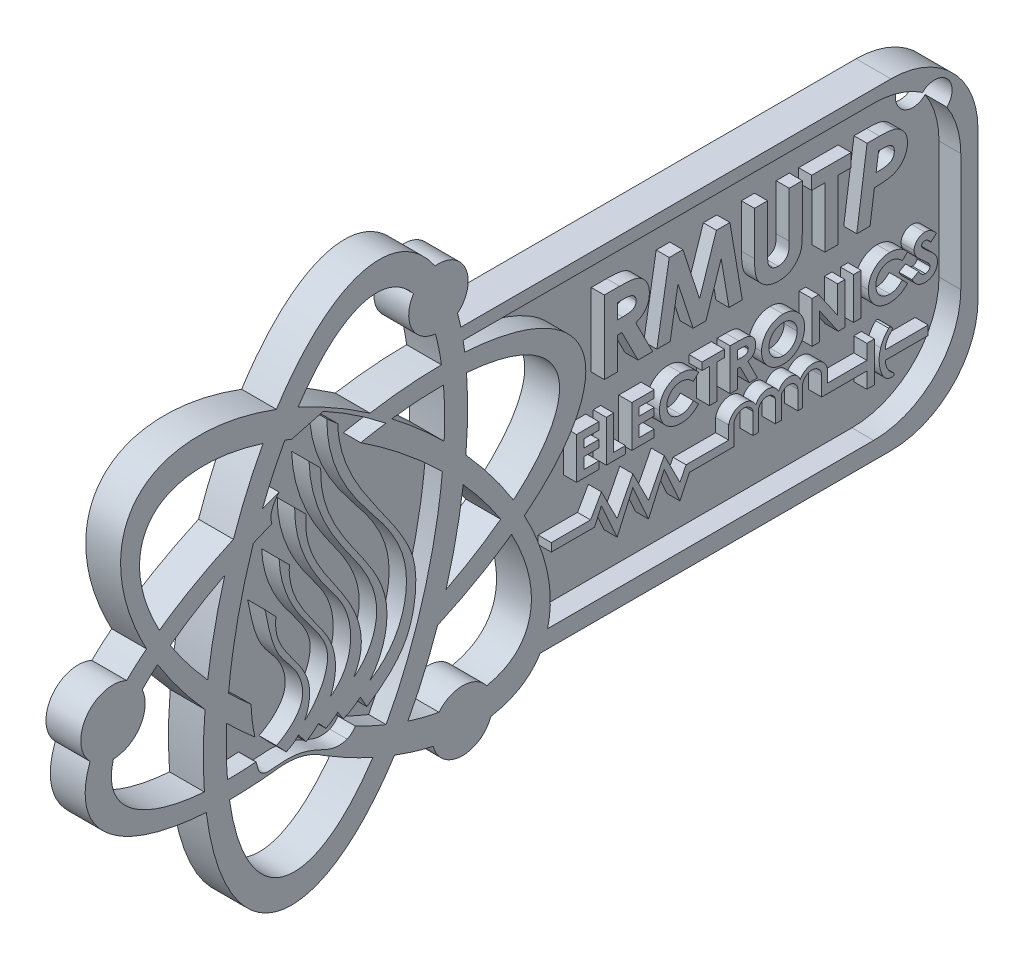
SolidWorks part; units mm, degrees
ref_plane "Front Plane" through (0, 0, 0) normal (0, 0, 1) x (1, 0, 0)
ref_plane "Top Plane" through (0, 0, 0) normal (0, 1, 0) x (1, 0, 0)
ref_plane "Right Plane" through (0, 0, 0) normal (1, 0, 0) x (0, 0, -1)
sketch "Sketch1" plane through (0, 0, 0) normal (1, 0, 0) x (0, 0, -1)
  line L0 (23.6962, 46.7228) -> (27.3509, 47.6931)
  line L1 (21.9568, 17.1343) -> (23.0925, 15.9422)
  line L2 (21.9056, 29.9851) -> (20.6519, 31.301)
  line L3 (24.4923, 16.9403) -> (25.3704, 15.8154)
  line L4 (23.4377, 34.3906) -> (22.2663, 35.562)
  line L5 (26.7972, 16.9366) -> (27.6441, 16.0073)
  line L6 (25.3704, 38.4449) -> (24.0506, 39.7647)
  line L7 (29.0048, 16.9366) -> (29.6488, 15.9422)
  line L8 (27.0464, 42.1977) -> (25.7038, 43.5403)
  line L9 (31.5987, 17.1343) -> (32.348, 15.8154)
  line L10 (29.0048, 45.6308) -> (27.7564, 46.7228)
  line L11 (92.5343, 48.1604) -> (43.1353, 48.1604)
  line L12 (43.3991, 46.7228) -> (90.5555, 46.7228)
  line L13 (53.1032, 13.1936) -> (90.5555, 13.1936)
  line L14 (92.5343, 11.1778) -> (52.2536, 11.1778)
  line L15 (100.5555, 36.7228) -> (100.5555, 23.1936)
  line L16 (102.5343, 38.1604) -> (102.5343, 21.1778)
  line L17 (54.5274, 20.5402) -> (59.0384, 20.5402)
  line L18 (59.0384, 20.5402) -> (60.2828, 22.7138)
  line L19 (60.2828, 22.7138) -> (62.0872, 19.1481)
  line L20 (62.0872, 19.1481) -> (63.8916, 22.7138)
  line L21 (63.8916, 22.7138) -> (65.696, 19.1481)
  line L22 (65.696, 19.1481) -> (67.5004, 22.7138)
  line L23 (67.5004, 22.7138) -> (69.3048, 19.1481)
  line L24 (69.3048, 19.1481) -> (70.0092, 20.5402)
  line L25 (70.0092, 20.5402) -> (74.9046, 20.5402)
  line L26 (74.9046, 20.5402) -> (74.9046, 22.0506)
  line L27 (86.2271, 22.0402) -> (86.2271, 20.5402)
  line L28 (86.2271, 20.5402) -> (90.7709, 20.5402)
  line L29 (90.7709, 20.5402) -> (90.7709, 22.2398)
  line L30 (90.7709, 22.2398) -> (91.6419, 22.2398)
  line L31 (91.6419, 22.2398) -> (91.6419, 17.6666)
  line L32 (91.6419, 17.6666) -> (90.7709, 17.6666)
  line L33 (90.7709, 17.6666) -> (90.7709, 19.4944)
  line L34 (90.7709, 19.4944) -> (85.5754, 19.4944)
  line L35 (85.5754, 19.4944) -> (85.5754, 21.6328)
  line L36 (83.3666, 21.6328) -> (83.3666, 19.4944)
  line L37 (83.3666, 19.4944) -> (82.8377, 19.4944)
  line L38 (82.8377, 19.4944) -> (82.8377, 21.6328)
  line L39 (80.94, 22.016) -> (80.94, 19.4944)
  line L40 (80.94, 19.4944) -> (80.2556, 19.4944)
  line L41 (80.2556, 19.4944) -> (80.2556, 22.016)
  line L42 (78.3521, 22.016) -> (78.3521, 19.5952)
  line L43 (78.3521, 19.5952) -> (77.6963, 19.5952)
  line L44 (77.6963, 19.5952) -> (77.6963, 22.016)
  line L45 (75.5169, 22.016) -> (75.5169, 19.5952)
  line L46 (75.5169, 19.5952) -> (70.395, 19.5952)
  line L47 (70.395, 19.5952) -> (69.3048, 17.2964)
  line L48 (69.3048, 17.2964) -> (67.5004, 21.3428)
  line L49 (67.5004, 21.3428) -> (65.696, 17.2964)
  line L50 (65.696, 17.2964) -> (63.8916, 21.3428)
  line L51 (63.8916, 21.3428) -> (62.0872, 17.2964)
  line L52 (62.0872, 17.2964) -> (60.2828, 21.3428)
  line L53 (60.2828, 21.3428) -> (59.5035, 19.5952)
  line L54 (59.5035, 19.5952) -> (54.5274, 19.5952)
  line L55 (54.5274, 19.5952) -> (54.5274, 20.5402)
  line L56 (97.8121, 20.5402) -> (97.8121, 19.4944)
  line L57 (97.8121, 19.4944) -> (92.8938, 19.494)
  line L58 (97.8121, 20.5402) -> (92.8938, 20.5402)
  circle A0 centre (3.1888, 28.8629) radius 3.6979
  circle A1 centre (40.5669, 52.343) radius 3.415
  circle A2 centre (43.3293, 8.9222) radius 3.4798
  arc A3 (74.9046, 22.0506) -> (78.0389, 22.4837) centre (76.5456, 21.7327) cw
  arc A4 (78.0389, 22.4837) -> (80.6289, 22.4837) centre (79.3339, 22.016) cw
  arc A5 (80.6289, 22.4837) -> (83.1177, 22.4837) centre (81.8733, 22.0402) cw
  arc A6 (83.1177, 22.4837) -> (86.2271, 22.0402) centre (84.5827, 21.6328) cw
  arc A7 (85.5754, 21.6328) -> (83.3666, 21.6328) centre (84.471, 21.6328) ccw
  arc A8 (82.8377, 21.6328) -> (80.94, 22.016) centre (81.8403, 21.584) ccw
  arc A9 (78.3521, 22.016) -> (80.2556, 22.016) centre (79.3039, 21.6888) cw
  arc A10 (77.6963, 22.016) -> (75.5169, 22.016) centre (76.6066, 21.7319) ccw
  arc A11 (92.8938, 19.494) -> (93.8175, 17.7886) centre (94.9302, 19.4942) ccw
  arc A12 (93.8175, 17.7886) -> (93.7117, 17.433) centre (93.7117, 17.6266) cw
  arc A13 (93.7117, 17.433) -> (92.5895, 18.1243) centre (93.7117, 18.6897) cw
  arc A14 (92.5895, 18.1243) -> (92.3554, 20.992) centre (96.0082, 19.8468) cw
  arc A15 (92.8938, 20.5402) -> (93.5961, 22.016) centre (94.7955, 20.5402) cw
  arc A16 (93.5961, 22.016) -> (93.2801, 22.4837) centre (93.4174, 22.2359) ccw
  arc A18 (92.3554, 20.992) -> (93.2801, 22.4837) centre (95.7251, 19.9355) cw
  arc A19 (102.5343, 38.1604) -> (92.5343, 48.1604) centre (92.5343, 38.1604) ccw
  arc A20 (100.5555, 36.7228) -> (90.5555, 46.7228) centre (90.5555, 36.7228) ccw
  arc A21 (102.5343, 21.1778) -> (92.5343, 11.1778) centre (92.5343, 21.1778) cw
  arc A22 (90.5555, 13.1936) -> (100.5555, 23.1936) centre (90.5555, 23.1936) ccw
  ellipse E0 centre (28.7406, 29.9851) end of major axis (22.2663, 0.5488) minor radius 14.058
  ellipse E1 centre (28.7406, 29.9851) end of major axis (34.5292, 56.3041) minor radius 11.3856
  ellipse E2 centre (28.7406, 29.9851) end of major axis (51.6163, 10.3034) minor radius 14.1914
  ellipse E3 centre (28.7406, 29.9851) end of major axis (50.0209, 13.1936) minor radius 11.7978
  ellipse E4 centre (28.7406, 29.9851) end of major axis (57.2274, 38.4449) minor radius 13.6079
  ellipse E5 centre (28.7406, 29.9851) end of major axis (54.2548, 37.9197) minor radius 11.349
  spline S0 degree 2 poles (22.2663, 42.1977) (21.0135, 40.8058) (21.4478, 39.4148) knots 0 0 0 1 1 1
  spline S1 degree 2 poles (19.356, 16.6628) (19.7811, 14.2911) (21.436, 14.6977) knots 0 0 0 1 1 1
  spline S2 degree 2 poles (21.436, 14.6977) (24.8637, 15.2662) (27.4097, 13.4223) knots 0 0 0 1 1 1
  spline S3 degree 2 poles (27.4097, 13.4223) (30.6793, 12.5571) (31.293, 14.5416) knots 0 0 0 1 1 1
  spline S4 degree 2 poles (19.5664, 16.6782) (19.9876, 14.35) (21.656, 14.9718) knots 0 0 0 1 1 1
  spline S5 degree 2 poles (21.656, 14.9718) (24.8244, 15.4846) (27.3509, 13.7631) knots 0 0 0 1 1 1
  spline S6 degree 2 poles (27.3509, 13.7631) (30.0432, 12.9512) (31.032, 14.564) knots 0 0 0 1 1 1
  spline S7 degree 2 poles (19.0361, 22.7138) (19.1097, 20.8704) (19.5166, 19.0857) knots 0 0 0 1 1 1
  spline S8 degree 2 poles (27.3509, 47.6931) (31.15, 45.6115) (34.5292, 42.9161) knots 0 0 0 1 1 1
  spline S9 degree 3 poles (23.0925, 15.9422) (25.1426, 16.7743) (26.5105, 20.4062) (23.9585, 25.1282) (21.5657, 27.2516) (21.9056, 29.9851) knots 0 0 0 0 0.409005 0.565398 1 1 1 1
  spline S10 degree 3 poles (20.6519, 31.301) (21.0409, 29.5256) (21.5089, 26.245) (24.5457, 23.4869) (25.5252, 19.562) (23.0914, 17.7006) (21.9568, 17.1343) knots 0 0 0 0 0.348086 0.55065 0.740127 1 1 1 1
  spline S11 degree 3 poles (25.3704, 15.8154) (26.5671, 16.5271) (28.1711, 18.2701) (28.9308, 21.4365) (28.4128, 24.3902) (25.5621, 28.2819) (23.284, 31.4433) (23.4377, 34.3906) knots 0 0 0 0 0.199231 0.318992 0.453693 0.61137 1 1 1 1
  spline S12 degree 3 poles (22.2663, 35.562) (22.3523, 32.9647) (23.9105, 29.3607) (26.7995, 26.067) (28.6177, 22.3416) (26.6581, 19.2421) (25.1944, 17.9781) knots 0 0 0 0 0.387463 0.576738 0.669072 1 1 1 1
  spline S13 degree 3 poles (27.6441, 16.0073) (29.0202, 16.6504) (30.4301, 18.5162) (31.8204, 21.4141) (31.431, 28.6461) (24.7665, 32.5876) (25.3704, 38.4449) knots 0 0 0 0 0.174679 0.271286 0.375272 1 1 1 1
  spline S14 degree 3 poles (24.0506, 39.7647) (24.0305, 36.0346) (26.1454, 31.8543) (31.0175, 25.9387) (30.9297, 20.887) (28.1533, 18.8928) knots 0 0 0 0 0.46113 0.600573 1 1 1 1
  spline S15 degree 3 poles (29.6488, 15.9422) (31.3065, 16.644) (34.1692, 19.3119) (35.0772, 24.4883) (33.3853, 28.7456) (29.7129, 33.7832) (26.9208, 38.1854) (27.0464, 42.1977) knots 0 0 0 0 0.178725 0.375481 0.48122 0.631471 1 1 1 1
  spline S16 degree 3 poles (25.7038, 43.5403) (25.8207, 39.8993) (28.0119, 34.7465) (32.4642, 29.3611) (34.1504, 24.0461) (32.3625, 20.584) (30.8598, 19.4944) knots 0 0 0 0 0.402185 0.614649 0.789436 1 1 1 1
  spline S17 degree 3 poles (32.348, 15.8154) (34.058, 16.9114) (36.7909, 19.1454) (38.0732, 23.9132) (38.0303, 27.5733) (36.2635, 31.1908) (32.4653, 36.4594) (29.1308, 41.3479) (29.0048, 45.6308) knots 0 0 0 0 0.182443 0.288353 0.426021 0.493148 0.639077 1 1 1 1
  spline S18 degree 3 poles (27.7564, 46.7228) (27.7075, 42.8969) (30.1891, 37.7297) (34.8197, 32.5778) (38.0232, 26.1659) (36.1553, 20.2641) (32.6863, 18.2305) knots 0 0 0 0 0.344411 0.51815 0.647215 1 1 1 1
  point P147 (0, 0)
  point P226 (22.3484, 25.869)
  point P227 (0, 0)
  point P228 (24.3272, 23.198)
  dimension "D4" = 10
  dimension "D1" = 0
  dimension "D2" = 1.0458
  dimension "D3" = 1.0458
extrude "Boss-Extrude4" add sketch "Sketch1" along normal blind 4
sketch "Sketch2" plane through (0, 0, 0) normal (-1, 0, 0) x (0, 0, 1)
  line L0 (-38.4272, 18.8191) -> (-35.025, 11.6982)
  line L1 (-35.025, 11.6982) -> (-31.9838, 13.1512)
  line L2 (-31.9838, 13.1512) -> (-28.9319, 13.1512)
  line L3 (-28.9319, 13.1512) -> (-27.2015, 13.7077)
  line L4 (-27.2015, 13.7077) -> (-26.3769, 14.1839)
  line L5 (-26.3769, 14.1839) -> (-25.111, 14.6833)
  line L6 (-25.111, 14.6833) -> (-23.3573, 14.9736)
  line L7 (-23.3573, 14.9736) -> (-21.6849, 14.8284)
  line L8 (-21.6849, 14.8284) -> (-21.0683, 14.7365)
  line L9 (-21.0683, 14.7365) -> (-19.8357, 14.9406)
  line L10 (-19.8357, 14.9406) -> (-15.2691, 15.9736)
  line L11 (-15.2691, 15.9736) -> (-15.7616, 23.4154)
  line L12 (-15.7616, 23.4154) -> (-15.7616, 26.1798)
  line L13 (-15.7616, 26.1798) -> (-17.5524, 36.9963)
  line L14 (-17.5524, 36.9963) -> (-21.9965, 48.2616)
  line L15 (-21.9965, 48.2616) -> (-23.3573, 48.8525)
  line L16 (-23.3573, 48.8525) -> (-26.5215, 48.1367)
  line L17 (-26.5215, 48.1367) -> (-27.5413, 47.7344)
  line L18 (-27.5413, 47.7344) -> (-34.227, 43.6322)
  line L19 (-34.227, 43.6322) -> (-35.8407, 41.8818)
  line L20 (-35.8407, 41.8818) -> (-42.4782, 34.6818)
  line L21 (-42.4782, 34.6818) -> (-38.4272, 18.8191)
extrude "Boss-Extrude5" add sketch "Sketch2" against normal blind 2
sketch "Sketch3" plane through (0, 0, 0) normal (-1, 0, 0) x (0, 0, 1)
  line L0 (-97.8015, 44.6933) -> (-101.3187, 39.7906)
  line L1 (-101.3187, 39.7906) -> (-101.3187, 20.4995)
  line L2 (-101.3187, 20.4995) -> (-97.8015, 14.4244)
  line L3 (-97.8015, 14.4244) -> (-92.7922, 12.1862)
  line L4 (-92.7922, 12.1862) -> (-52.0784, 12.1862)
  line L5 (-52.0784, 12.1862) -> (-52.0784, 20.4995)
  line L6 (-52.0784, 20.4995) -> (-49.575, 26.1023)
  line L7 (-49.575, 26.1023) -> (-54.6363, 32.1168)
  line L8 (-54.6363, 32.1168) -> (-55.3824, 37.8721)
  line L9 (-55.3824, 37.8721) -> (-53.6915, 41.6565)
  line L10 (-53.6915, 41.6565) -> (-44.4046, 44.0538)
  line L11 (-44.4046, 44.0538) -> (-42.6993, 44.0538)
  line L12 (-42.6993, 44.0538) -> (-42.6993, 47.7841)
  line L13 (-42.6993, 47.7841) -> (-93.6575, 47.2684)
  line L14 (-93.6575, 47.2684) -> (-98.0208, 44.3876)
  line L15 (-98.0208, 44.3876) -> (-97.8015, 44.6933)
extrude "Boss-Extrude6" add sketch "Sketch3" against normal blind 1.5 contours L13 L14 L0 L1 L2 L3 L4 L5 L6 L7 L8 L9 L10 L11 L12
sketch "Sketch4" plane through (1.5, 0, 0) normal (1, 0, 0) x (0, 0, -1)
  text T0 "<b>RMUT<i>P</i></b>" font "Century Gothic" height 8.4083
sketch "Sketch5" plane through (1.5, 0, 0) normal (1, 0, 0) x (0, 0, -1)
  text T0 "<b>ELECTRONICS</b>" font "Century Gothic" height in points 18
sketch "Sketch6" plane through (1.5, 0, 0) normal (1, 0, 0) x (0, 0, -1)
  circle A0 centre (97.5569, 43.5516) radius 2
extrude "Cut-Extrude2" cut sketch "Sketch6" against normal mid plane 5
sketch "Sketch7" plane through (2, 0, 0) normal (1, 0, 0) x (0, 0, -1)
  line L0 (19.5664, 16.6782) -> (19.6263, 16.6782)
  line L2 (27.3509, 47.6931) -> (23.6962, 46.7228)
  ellipse E13 centre (28.7406, 29.9851) end of major axis (50.0209, 13.1936) minor radius 11.7978 (31.0182, 14.5416) -> (34.5528, 12.9287) ccw
  ellipse E14 centre (28.7406, 29.9851) end of major axis (34.5292, 56.3041) minor radius 11.3856 (34.5528, 12.9287) -> (41.0231, 34.8669) ccw
  ellipse E15 centre (28.7406, 29.9851) end of major axis (50.0209, 13.1936) minor radius 11.7978 (41.0231, 34.8669) -> (31.6425, 42.4197) ccw
  ellipse E16 centre (28.7406, 29.9851) end of major axis (54.2548, 37.9197) minor radius 11.349 (34.5292, 42.9161) -> (31.6425, 42.4197) ccw
  ellipse E17 centre (28.7406, 29.9851) end of major axis (50.0209, 13.1936) minor radius 11.7978 (23.6962, 46.7228) -> (22.9283, 47.0415) ccw
  ellipse E18 centre (28.7406, 29.9851) end of major axis (34.5292, 56.3041) minor radius 11.3856 (22.9283, 47.0415) -> (20.3581, 41.5081) ccw
  ellipse E19 centre (28.7406, 29.9851) end of major axis (57.2274, 38.4449) minor radius 13.6079 (22.2663, 42.1977) -> (20.3581, 41.5081) ccw
  ellipse E20 centre (28.7406, 29.9851) end of major axis (54.2548, 37.9197) minor radius 11.349 (21.436, 39.4534) -> (19.3044, 38.5834) ccw
  ellipse E21 centre (28.7406, 29.9851) end of major axis (34.5292, 56.3041) minor radius 11.3856 (19.3044, 38.5834) -> (16.458, 25.1033) ccw
  ellipse E22 centre (28.7406, 29.9851) end of major axis (50.0209, 13.1936) minor radius 11.7978 (16.458, 25.1033) -> (19.0361, 22.7138) ccw
  ellipse E23 centre (28.7406, 29.9851) end of major axis (51.6163, 10.3034) minor radius 14.1914 (16.2535, 22.207) -> (19.4849, 19.2274) ccw
  ellipse E24 centre (28.7406, 29.9851) end of major axis (34.5292, 56.3041) minor radius 11.3856 (16.2535, 22.207) -> (16.3371, 16.5539) ccw
  ellipse E25 centre (28.7406, 29.9851) end of major axis (54.2548, 37.9197) minor radius 11.349 (16.3371, 16.5539) -> (19.5664, 16.6782) ccw
  parabola Q6 (21.656, 14.9718) -> (27.3509, 13.7631) focus (24.1608, 11.3161) apex (25.1624, 14.8017)
  parabola Q7 (27.3509, 13.7631) -> (31.0182, 14.5416) focus (29.8365, 14.7345) apex (30.4213, 13.9022)
  parabola Q8 (34.5292, 42.9161) -> (27.3509, 47.6931) focus (17.4671, 24.4734) apex (31.5792, 45.0975)
  parabola Q9 (22.2663, 42.1977) -> (21.436, 39.4534) focus (22.4832, 40.1303) apex (21.336, 40.1297)
  parabola Q10 (19.0361, 22.7138) -> (19.4849, 19.2274) focus (29.0465, 21.7652) apex (19.3213, 20.0531)
  parabola Q11 (19.5664, 16.6782) -> (21.656, 14.9718) focus (20.7679, 15.4088) apex (20.5641, 14.9269)
  parabola Q17 (19.5664, 16.6782) -> (21.656, 14.9718) focus (20.7679, 15.4088) apex (20.5641, 14.9269)
  spline S0 degree 3 poles (19.6263, 16.6782) (19.7789, 16.2657) (19.8824, 14.9325) (21.2114, 14.8663) (21.656, 14.9718) knots 0 0 0 0 0.506588 1 1 1 1
  dimension "D1" = 0
extrude "Boss-Extrude9" add sketch "Sketch7" along normal mid plane 4 contours Q17 S0 L0
sketch "Sketch8" plane through (2, 0, 0) normal (1, 0, 0) x (0, 0, -1)
  line L0 (19.9524, 15.6156) -> (19.657, 15.5586)
  line L1 (19.9291, 15.6569) -> (19.7467, 15.5098)
  line L2 (19.7467, 15.5098) -> (20.3414, 14.9054)
  line L3 (20.3414, 14.9054) -> (21.3009, 14.8043)
  line L4 (21.3009, 14.8043) -> (22.0762, 14.8695)
  line L5 (22.0762, 14.8695) -> (22.9816, 14.9455)
  line L6 (22.9816, 14.9455) -> (23.3427, 14.9075)
  line L7 (23.3427, 14.9075) -> (24.9373, 14.7395)
  line L8 (24.9373, 14.7395) -> (26.5205, 14.1237)
  line L9 (26.5205, 14.1237) -> (27.2626, 13.6388)
  line L10 (27.2626, 13.6388) -> (27.914, 13.4772)
  line L11 (27.914, 13.4772) -> (29.6332, 13.2962)
  line L12 (29.6332, 13.2962) -> (30.0883, 13.712)
  parabola Q0 (27.3509, 13.7631) -> (31.0182, 14.5416) focus (29.8365, 14.7345) apex (30.4213, 13.9022) construction
  spline S0 degree 3 poles (19.9291, 15.6569) (20.2492, 15.071) (20.9893, 14.9824) (22.1928, 15.1048) (23.4525, 15.2259) (24.9896, 14.9959) (27.1712, 14.2333) (28.6603, 13.2263) (30.0883, 13.712) knots 0 0 0 0 0.141392 0.207476 0.344375 0.500031 0.644903 1 1 1 1
  spline S1 degree 3 poles (19.6263, 16.6782) (19.7789, 16.2657) (19.8824, 14.9325) (21.2114, 14.8663) (21.656, 14.9718) knots 0 0 0 0 0.506588 1 1 1 1 construction
  spline M27 degree 3 poles (19.6263, 16.6782) (19.7789, 16.2657) (19.8824, 14.9325) (21.2114, 14.8663) (21.656, 14.9718) knots 0 0 0 0 0.506588 1 1 1 1
  spline M28 degree 2 poles (21.656, 14.9718) (24.8244, 15.4846) (27.3509, 13.7631) knots 0 0 0 1 1 1
  spline M29 degree 2 poles (27.3509, 13.7631) (30.0432, 12.9512) (31.032, 14.564) knots 0 0 0 1 1 1 only from (27.3509, 13.7631) to (31.0182, 14.5416)
extrude "Boss-Extrude10" add sketch "Sketch8" along normal mid plane 4 contours S0 L0 M27 M28 M29
extrude "Boss-Extrude12" add sketch "Sketch4" along normal blind 1.5
extrude "Boss-Extrude13" add sketch "Sketch5" along normal blind 1.5
sketch "Sketch9" plane through (4, 0, 0) normal (1, 0, 0) x (0, 0, -1)
  line L0 (54.145, 21.3657) -> (54.145, 18.5233)
  line L1 (54.145, 18.5233) -> (60.5607, 16.9261)
  line L2 (60.5607, 16.9261) -> (74.0419, 15.5726)
  line L3 (74.0419, 15.5726) -> (95.9692, 16.9261)
  line L4 (95.9692, 16.9261) -> (98.947, 19.4708)
  line L5 (98.947, 19.4708) -> (97.8641, 21.6364)
  line L6 (97.8641, 21.6364) -> (92.4635, 23.4366)
  line L7 (92.4635, 23.4366) -> (71.2266, 23.9916)
  line L8 (71.2266, 23.9916) -> (55.144, 22.5365)
  line L9 (55.144, 22.5365) -> (54.145, 21.3657)
extrude "Cut-Extrude3" cut sketch "Sketch9" against normal blind 1
